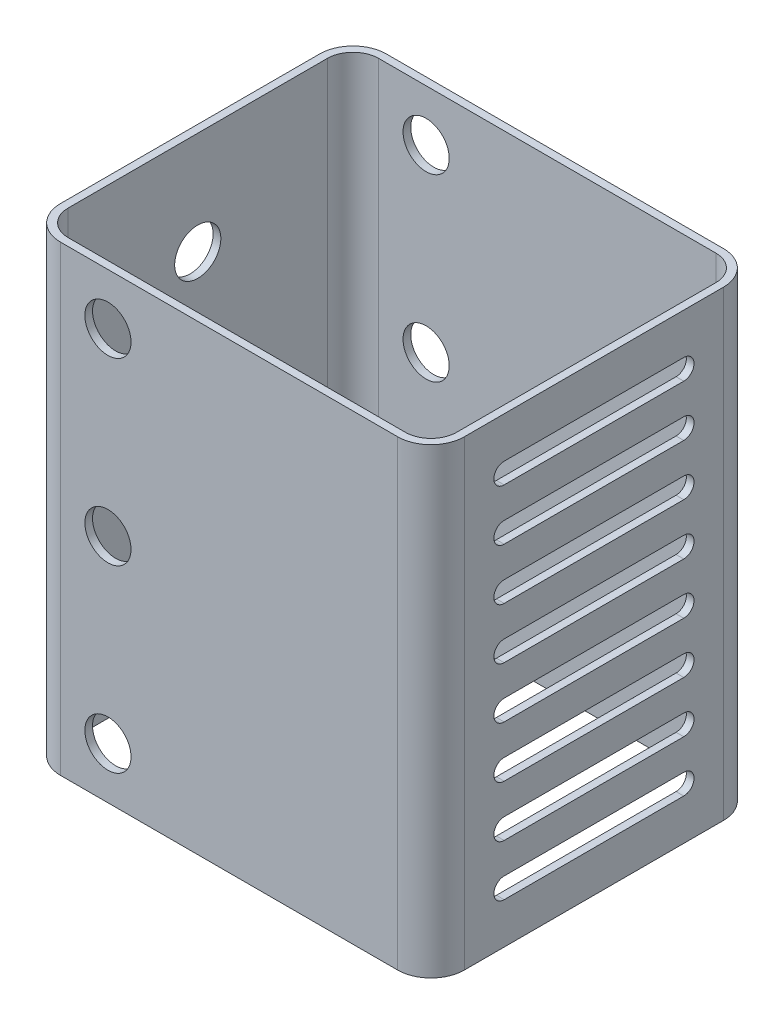
SolidWorks part; units mm, degrees
ref_plane "Front Plane" through (0, 0, 0) normal (0, 0, 1) x (1, 0, 0)
ref_plane "Top Plane" through (0, 0, 0) normal (0, 1, 0) x (1, 0, 0)
ref_plane "Right Plane" through (0, 0, 0) normal (1, 0, 0) x (0, 0, -1)
sketch "Sketch1" plane through (0, 0, 0) normal (0, 1, 0) x (1, 0, 0)
  line L0 (-32.85, -31.75) -> (32.85, -31.75)
  line L1 (-32.85, -30.25) -> (32.85, -30.25)
  line L2 (-37.85, -25.25) -> (-37.85, 25.25)
  line L3 (-32.85, 30.25) -> (32.85, 30.25)
  line L4 (37.85, -25.25) -> (37.85, 25.25)
  line L5 (-37.85, -30.25) -> (37.85, 30.25) construction
  line L6 (-37.85, 30.25) -> (37.85, -30.25) construction
  line L7 (39.35, -25.25) -> (39.35, 25.25)
  line L8 (-32.85, 31.75) -> (32.85, 31.75)
  line L9 (-39.35, -25.25) -> (-39.35, 25.25)
  arc A0 (32.85, 30.25) -> (37.85, 25.25) centre (32.85, 25.25) cw
  arc A1 (32.85, -30.25) -> (37.85, -25.25) centre (32.85, -25.25) ccw
  arc A2 (-32.85, -30.25) -> (-37.85, -25.25) centre (-32.85, -25.25) cw
  arc A3 (-37.85, 25.25) -> (-32.85, 30.25) centre (-32.85, 25.25) cw
  arc A4 (32.85, -31.75) -> (39.35, -25.25) centre (32.85, -25.25) ccw
  arc A5 (32.85, 31.75) -> (39.35, 25.25) centre (32.85, 25.25) cw
  arc A6 (-39.35, 25.25) -> (-32.85, 31.75) centre (-32.85, 25.25) cw
  arc A7 (-32.85, -31.75) -> (-39.35, -25.25) centre (-32.85, -25.25) cw
  point P0 (0, 0)
  dimension "D1" = 5
  dimension "D2" = 50.5
  dimension "D3" = 65.7
  dimension "D4" = 1.5
extrude "Boss-Extrude1" add sketch "Sketch1" along normal blind 90
sketch "Sketch2" plane through (-34.75, 0, 0) normal (-1, 0, 0) x (0, 0, 1)
  line L0 (0, 90) -> (0, 0) construction
  line L1 (-25.25, 90) -> (25.25, 90) construction
  line L2 (-25.25, 0) -> (25.25, 0) construction
  circle A0 centre (0, 70) radius 4.5
  circle A1 centre (0, 20) radius 4.5
  point P10 (0, 45)
  dimension "D1" = 9
  dimension "D2" = 9
  dimension "D3" = 50
  dimension "D4" = 25
extrude "Cut-Extrude1" cut sketch "Sketch2" along normal blind 17
sketch "Sketch3" plane through (0, 0, 32.25) normal (0, 0, 1) x (1, 0, 0)
  line L0 (-23.6, 90) -> (-23.6, 0) construction
  line L1 (-27.75, 90) -> (27.75, 90) construction
  line L2 (-27.75, 0) -> (27.75, 0) construction
  line L4 (-32.85, 90) -> (-32.85, 0) construction
  circle A0 centre (-23.6, 80) radius 4.5
  circle A1 centre (-23.6, 10) radius 4.5
  circle A2 centre (-23.6, 45) radius 4.5
  dimension "D2" = 9
  dimension "D1" = 9.25
  dimension "D3" = 70
  dimension "D4" = 35
extrude "Cut-Extrude2" cut sketch "Sketch3" against normal blind 95
sketch "Sketch4" plane through (34.75, 0, 0) normal (1, 0, 0) x (0, 0, -1)
  line L0 (-17.5, 80) -> (17.5, 80) construction
  line L1 (-17.5, 82) -> (17.5, 82)
  line L2 (-17.5, 78) -> (17.5, 78)
  line L3 (0, 80) -> (0, 90) construction
  line L4 (-25.25, 90) -> (25.25, 90) construction
  line L5 (-17.5, 70) -> (17.5, 70) construction
  line L6 (-17.5, 72) -> (17.5, 72)
  line L7 (-17.5, 68) -> (17.5, 68)
  line L8 (-17.5, 60) -> (17.5, 60) construction
  line L9 (-17.5, 62) -> (17.5, 62)
  line L10 (-17.5, 58) -> (17.5, 58)
  line L11 (-17.5, 50) -> (17.5, 50) construction
  line L12 (-17.5, 52) -> (17.5, 52)
  line L13 (-17.5, 48) -> (17.5, 48)
  line L14 (-17.5, 40) -> (17.5, 40) construction
  line L15 (-17.5, 42) -> (17.5, 42)
  line L16 (-17.5, 38) -> (17.5, 38)
  line L17 (-17.5, 30) -> (17.5, 30) construction
  line L18 (-17.5, 32) -> (17.5, 32)
  line L19 (-17.5, 28) -> (17.5, 28)
  line L20 (-17.5, 20) -> (17.5, 20) construction
  line L21 (-17.5, 22) -> (17.5, 22)
  line L22 (-17.5, 18) -> (17.5, 18)
  line L23 (-17.5, 10) -> (17.5, 10) construction
  line L24 (-17.5, 12) -> (17.5, 12)
  line L25 (-17.5, 8) -> (17.5, 8)
  arc A0 (-17.5, 82) -> (-17.5, 78) centre (-17.5, 80) ccw
  arc A1 (17.5, 78) -> (17.5, 82) centre (17.5, 80) ccw
  arc A2 (-17.5, 72) -> (-17.5, 68) centre (-17.5, 70) ccw
  arc A3 (17.5, 68) -> (17.5, 72) centre (17.5, 70) ccw
  arc A4 (-17.5, 62) -> (-17.5, 58) centre (-17.5, 60) ccw
  arc A5 (17.5, 58) -> (17.5, 62) centre (17.5, 60) ccw
  arc A6 (-17.5, 52) -> (-17.5, 48) centre (-17.5, 50) ccw
  arc A7 (17.5, 48) -> (17.5, 52) centre (17.5, 50) ccw
  arc A8 (-17.5, 42) -> (-17.5, 38) centre (-17.5, 40) ccw
  arc A9 (17.5, 38) -> (17.5, 42) centre (17.5, 40) ccw
  arc A10 (-17.5, 32) -> (-17.5, 28) centre (-17.5, 30) ccw
  arc A11 (17.5, 28) -> (17.5, 32) centre (17.5, 30) ccw
  arc A12 (-17.5, 22) -> (-17.5, 18) centre (-17.5, 20) ccw
  arc A13 (17.5, 18) -> (17.5, 22) centre (17.5, 20) ccw
  arc A14 (-17.5, 12) -> (-17.5, 8) centre (-17.5, 10) ccw
  arc A15 (17.5, 8) -> (17.5, 12) centre (17.5, 10) ccw
  point P2 (0, 80)
  point P15 (0, 70)
  point P22 (0, 60)
  point P29 (0, 50)
  point P36 (0, 40)
  point P43 (0, 30)
  point P50 (0, 20)
  point P57 (0, 10)
  dimension "D1" = 2
  dimension "D2" = 35
  dimension "D3" = 10
  dimension "D4" = 8
extrude "Cut-Extrude3" cut sketch "Sketch4" along normal blind 29
